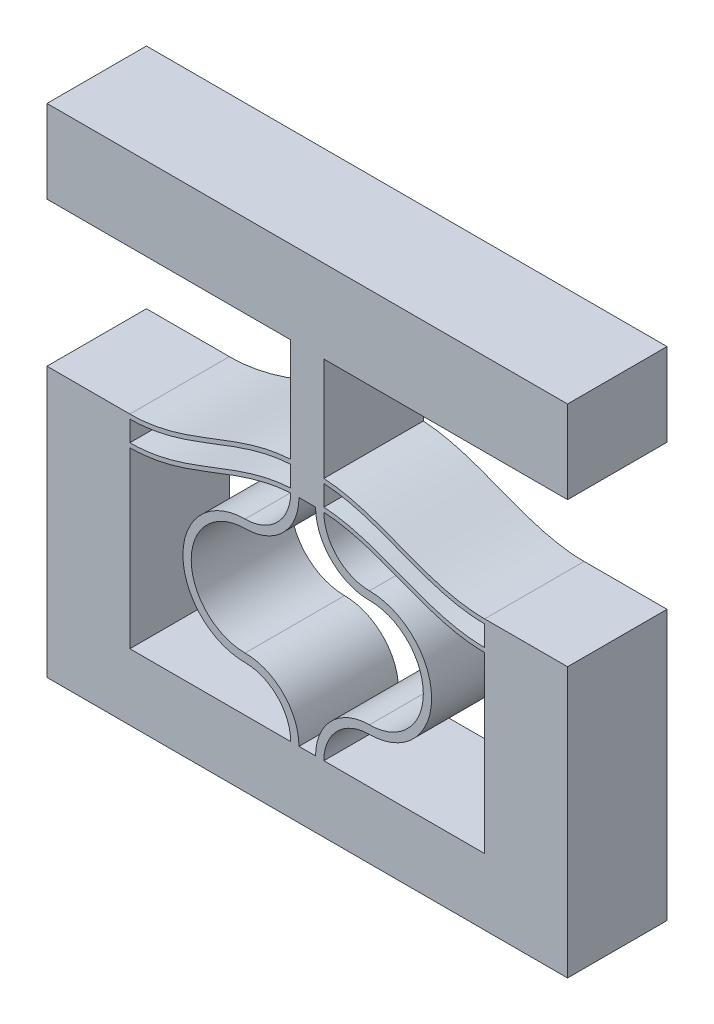
SolidWorks part; units mm, degrees
ref_plane "Front Plane" through (0, 0, 0) normal (0, 0, 1) x (1, 0, 0)
ref_plane "Top Plane" through (0, 0, 0) normal (0, 1, 0) x (1, 0, 0)
ref_plane "Right Plane" through (0, 0, 0) normal (1, 0, 0) x (0, 0, -1)
sketch "Sketch1" plane through (0, 0, 0) normal (0, 0, 1) x (1, 0, 0)
  line L4 (0, 10.5) -> (0, 0)
  line L5 (10.2, 0) -> (10.2, 13) construction
  line L6 (10.2, 13) -> (10.2, 15.9852) construction
  line L17 (9.7, 0) -> (0, 0)
  line L18 (10.7, 0) -> (20.4, 0)
  line L19 (20.4, 0) -> (20.4, 10.5)
  line L20 (10.7, 13.2452) -> (10.7, 14.4852)
  line L21 (9.7, 13.2452) -> (9.7, 14.4852)
  line L22 (10.7, 14.7452) -> (10.7, 15.9852)
  line L23 (10.7, 15.9852) -> (9.7, 15.9852)
  line L24 (9.7, 15.9852) -> (9.7, 14.7452)
  line L31 (-5, 12.26) -> (-5, -4)
  line L32 (-5, -4) -> (25.4, -4)
  line L33 (25.4, -4) -> (25.4, 12.26)
  line L34 (0, 10.76) -> (0, 12)
  line L36 (-5, 12.26) -> (0, 12.26)
  line L37 (25.4, 12.26) -> (20.4, 12.26)
  line L38 (20.4, 10.76) -> (20.4, 12)
  arc A0 (10.2, 13) -> (6.95, 9.75) centre (6.95, 13) cw
  arc A1 (6.95, 9.75) -> (6.95, 3.25) centre (6.95, 6.5) ccw
  arc A2 (6.95, 3.25) -> (10.2, 0) centre (6.95, 0) cw
  arc A3 (9.7, 12.9852) -> (6.95, 10.25) centre (6.95, 13) cw
  arc A4 (6.95, 10.25) -> (6.95, 2.75) centre (6.95, 6.5) ccw
  arc A5 (6.95, 2.75) -> (9.7, 0) centre (6.95, 0) cw
  arc A6 (9.7, 13) -> (6.95, 10.25) centre (6.95, 13) cw construction
  arc A7 (13.45, 3.25) -> (10.2, 0) centre (13.45, 0) ccw
  arc A8 (13.45, 2.75) -> (10.7, 0) centre (13.45, 0) ccw
  arc A9 (13.45, 9.75) -> (13.45, 3.25) centre (13.45, 6.5) cw
  arc A10 (13.45, 10.25) -> (13.45, 2.75) centre (13.45, 6.5) cw
  arc A11 (10.7, 12.9852) -> (13.45, 10.25) centre (13.45, 13) ccw
  arc A12 (10.2, 13) -> (13.45, 9.75) centre (13.45, 13) ccw
  spline S0 degree 4 poles (-2.0399, 10.9987) (-1.9769, 10.9844) (-1.8506, 10.9568) (-1.6594, 10.9185) (-1.4063, 10.8738) (-1.1473, 10.836) (-0.8994, 10.8056) (-0.6275, 10.7825) (-0.4084, 10.7671) (-0.0945, 10.7598) (0.0489, 10.7593) (0.3554, 10.7653) (0.5833, 10.7785) (0.8327, 10.7992) (1.1232, 10.8326) (1.4148, 10.8743) (1.7521, 10.9345) (2.2064, 11.0333) (2.726, 11.1697) (3.2397, 11.3281) (3.7479, 11.5024) (4.1845, 11.6613) (4.5513, 11.7992) (4.9172, 11.9395) (5.2828, 12.0805) (5.7402, 12.2559) (6.427, 12.5125) (7.2136, 12.7819) (8.1107, 13.0284) (9.0261, 13.1932) (9.8075, 13.2661) (10.5925, 13.2661) (11.3739, 13.1932) (12.2893, 13.0284) (13.1864, 12.7819) (13.973, 12.5125) (14.6598, 12.2559) (15.2087, 12.0455) (15.6656, 11.8688) (16.1235, 11.6948) (16.6521, 11.5024) (17.1603, 11.3281) (17.6739, 11.1697) (18.1937, 11.0333) (18.5999, 10.9449) (18.8889, 10.8915) (19.1309, 10.8534) (19.3251, 10.827) (19.5196, 10.8048) (19.7158, 10.7868) (19.909, 10.7733) (20.1017, 10.7642) (20.3513, 10.7593) (20.4943, 10.7598) (20.8085, 10.7671) (21.0274, 10.7825) (21.2994, 10.8056) (21.5473, 10.836) (21.8063, 10.8738) (22.0594, 10.9185) (22.2506, 10.9568) (22.3769, 10.9844) (22.4399, 10.9987) knots 0 0 0 0 0 0.010251 0.020502 0.030753 0.041005 0.05113 0.061255 0.071381 0.081506 0.089265 0.097024 0.112543 0.120302 0.128061 0.143579 0.159098 0.174616 0.201648 0.22868 0.244198 0.259716 0.275235 0.290753 0.306271 0.32179 0.352826 0.40689 0.437927 0.468963 0.5 0.531037 0.562073 0.59311 0.647174 0.67821 0.693729 0.709247 0.740284 0.755802 0.77132 0.798352 0.825384 0.840902 0.856421 0.86418 0.871939 0.879698 0.887457 0.895217 0.902976 0.910735 0.918494 0.928619 0.938745 0.94887 0.958995 0.969247 0.979498 0.989749 1 1 1 1 1 construction
  spline S1 degree 4 poles (0, 10.76) (0.041, 10.76) (0.1243, 10.7608) (0.3554, 10.7653) (0.5833, 10.7785) (0.8327, 10.7992) (1.1232, 10.8326) (1.4148, 10.8743) (1.7521, 10.9345) (2.2064, 11.0333) (2.726, 11.1697) (3.2397, 11.3281) (3.7479, 11.5024) (4.1845, 11.6613) (4.5513, 11.7992) (4.9172, 11.9395) (5.2828, 12.0805) (5.7402, 12.2559) (6.427, 12.5125) (7.2136, 12.7819) (8.1107, 13.0284) (9.0261, 13.1932) (9.8075, 13.2661) (10.5925, 13.2661) (11.3739, 13.1932) (12.2893, 13.0284) (13.1864, 12.7819) (13.973, 12.5125) (14.6598, 12.2559) (15.2087, 12.0455) (15.6656, 11.8688) (16.1235, 11.6948) (16.6521, 11.5024) (17.1603, 11.3281) (17.6739, 11.1697) (18.1937, 11.0333) (18.5999, 10.9449) (18.8889, 10.8915) (19.1309, 10.8534) (19.3251, 10.827) (19.5196, 10.8048) (19.7158, 10.7868) (19.909, 10.7733) (20.1017, 10.7642) (20.2757, 10.7608) (20.359, 10.76) (20.4, 10.76) knots 0.081506 0.081506 0.081506 0.081506 0.081506 0.089265 0.097024 0.112543 0.120302 0.128061 0.143579 0.159098 0.174616 0.201648 0.22868 0.244198 0.259716 0.275235 0.290753 0.306271 0.32179 0.352826 0.40689 0.437927 0.468963 0.5 0.531037 0.562073 0.59311 0.647174 0.67821 0.693729 0.709247 0.740284 0.755802 0.77132 0.798352 0.825384 0.840902 0.856421 0.86418 0.871939 0.879698 0.887457 0.895217 0.902976 0.910735 0.918494 0.918494 0.918494 0.918494 0.918494
  spline S2 degree 4 poles (-2.0399, 12.2387) (-1.9769, 12.2244) (-1.8506, 12.1968) (-1.6594, 12.1585) (-1.4063, 12.1138) (-1.1473, 12.076) (-0.8994, 12.0456) (-0.6275, 12.0225) (-0.4084, 12.0071) (-0.0945, 11.9998) (0.0489, 11.9993) (0.3554, 12.0053) (0.5833, 12.0185) (0.8327, 12.0392) (1.1232, 12.0726) (1.4148, 12.1143) (1.7521, 12.1745) (2.2064, 12.2733) (2.726, 12.4097) (3.2397, 12.5681) (3.7479, 12.7424) (4.1845, 12.9013) (4.5513, 13.0392) (4.9172, 13.1795) (5.2828, 13.3205) (5.7402, 13.4959) (6.427, 13.7525) (7.2136, 14.0219) (8.1107, 14.2684) (9.0261, 14.4332) (9.8075, 14.5061) (10.5925, 14.5061) (11.3739, 14.4332) (12.2893, 14.2684) (13.1864, 14.0219) (13.973, 13.7525) (14.6598, 13.4959) (15.2087, 13.2855) (15.6656, 13.1088) (16.1235, 12.9348) (16.6521, 12.7424) (17.1603, 12.5681) (17.6739, 12.4097) (18.1937, 12.2733) (18.5999, 12.1849) (18.8889, 12.1315) (19.1309, 12.0934) (19.3251, 12.067) (19.5196, 12.0448) (19.7158, 12.0268) (19.909, 12.0133) (20.1017, 12.0042) (20.3513, 11.9993) (20.4943, 11.9998) (20.8085, 12.0071) (21.0274, 12.0225) (21.2994, 12.0456) (21.5473, 12.076) (21.8063, 12.1138) (22.0594, 12.1585) (22.2506, 12.1968) (22.3769, 12.2244) (22.4399, 12.2387) knots 0 0 0 0 0 0.010251 0.020502 0.030753 0.041005 0.05113 0.061255 0.071381 0.081506 0.089265 0.097024 0.112543 0.120302 0.128061 0.143579 0.159098 0.174616 0.201648 0.22868 0.244198 0.259716 0.275235 0.290753 0.306271 0.32179 0.352826 0.40689 0.437927 0.468963 0.5 0.531037 0.562073 0.59311 0.647174 0.67821 0.693729 0.709247 0.740284 0.755802 0.77132 0.798352 0.825384 0.840902 0.856421 0.86418 0.871939 0.879698 0.887457 0.895217 0.902976 0.910735 0.918494 0.928619 0.938745 0.94887 0.958995 0.969247 0.979498 0.989749 1 1 1 1 1 construction
  spline S3 degree 4 poles (0, 12) (0.041, 12) (0.1243, 12.0008) (0.3554, 12.0053) (0.5833, 12.0185) (0.8327, 12.0392) (1.1232, 12.0726) (1.4148, 12.1143) (1.7521, 12.1745) (2.2064, 12.2733) (2.726, 12.4097) (3.2397, 12.5681) (3.7479, 12.7424) (4.1845, 12.9013) (4.5513, 13.0392) (4.9172, 13.1795) (5.2828, 13.3205) (5.7402, 13.4959) (6.427, 13.7525) (7.2136, 14.0219) (8.1107, 14.2684) (9.0261, 14.4332) (9.8075, 14.5061) (10.5925, 14.5061) (11.3739, 14.4332) (12.2893, 14.2684) (13.1864, 14.0219) (13.973, 13.7525) (14.6598, 13.4959) (15.2087, 13.2855) (15.6656, 13.1088) (16.1235, 12.9348) (16.6521, 12.7424) (17.1603, 12.5681) (17.6739, 12.4097) (18.1937, 12.2733) (18.5999, 12.1849) (18.8889, 12.1315) (19.1309, 12.0934) (19.3251, 12.067) (19.5196, 12.0448) (19.7158, 12.0268) (19.909, 12.0133) (20.1017, 12.0042) (20.2757, 12.0008) (20.359, 12) (20.4, 12) knots 0.081506 0.081506 0.081506 0.081506 0.081506 0.089265 0.097024 0.112543 0.120302 0.128061 0.143579 0.159098 0.174616 0.201648 0.22868 0.244198 0.259716 0.275235 0.290753 0.306271 0.32179 0.352826 0.40689 0.437927 0.468963 0.5 0.531037 0.562073 0.59311 0.647174 0.67821 0.693729 0.709247 0.740284 0.755802 0.77132 0.798352 0.825384 0.840902 0.856421 0.86418 0.871939 0.879698 0.887457 0.895217 0.902976 0.910735 0.918494 0.918494 0.918494 0.918494 0.918494
  spline S4 degree 4 poles (-2.0399, 12.4987) (-1.9769, 12.4844) (-1.8506, 12.4568) (-1.6594, 12.4185) (-1.4063, 12.3738) (-1.1473, 12.336) (-0.8994, 12.3056) (-0.6275, 12.2825) (-0.4084, 12.2671) (-0.0945, 12.2598) (0.0489, 12.2593) (0.3554, 12.2653) (0.5833, 12.2785) (0.8327, 12.2992) (1.1232, 12.3326) (1.4148, 12.3743) (1.7521, 12.4345) (2.2064, 12.5333) (2.726, 12.6697) (3.2397, 12.8281) (3.7479, 13.0024) (4.1845, 13.1613) (4.5513, 13.2992) (4.9172, 13.4395) (5.2828, 13.5805) (5.7402, 13.7559) (6.427, 14.0125) (7.2136, 14.2819) (8.1107, 14.5284) (9.0261, 14.6932) (9.8075, 14.7661) (10.5925, 14.7661) (11.3739, 14.6932) (12.2893, 14.5284) (13.1864, 14.2819) (13.973, 14.0125) (14.6598, 13.7559) (15.2087, 13.5455) (15.6656, 13.3688) (16.1235, 13.1948) (16.6521, 13.0024) (17.1603, 12.8281) (17.6739, 12.6697) (18.1937, 12.5333) (18.5999, 12.4449) (18.8889, 12.3915) (19.1309, 12.3534) (19.3251, 12.327) (19.5196, 12.3048) (19.7158, 12.2868) (19.909, 12.2733) (20.1017, 12.2642) (20.3513, 12.2593) (20.4943, 12.2598) (20.8085, 12.2671) (21.0274, 12.2825) (21.2994, 12.3056) (21.5473, 12.336) (21.8063, 12.3738) (22.0594, 12.4185) (22.2506, 12.4568) (22.3769, 12.4844) (22.4399, 12.4987) knots 0 0 0 0 0 0.010251 0.020502 0.030753 0.041005 0.05113 0.061255 0.071381 0.081506 0.089265 0.097024 0.112543 0.120302 0.128061 0.143579 0.159098 0.174616 0.201648 0.22868 0.244198 0.259716 0.275235 0.290753 0.306271 0.32179 0.352826 0.40689 0.437927 0.468963 0.5 0.531037 0.562073 0.59311 0.647174 0.67821 0.693729 0.709247 0.740284 0.755802 0.77132 0.798352 0.825384 0.840902 0.856421 0.86418 0.871939 0.879698 0.887457 0.895217 0.902976 0.910735 0.918494 0.928619 0.938745 0.94887 0.958995 0.969247 0.979498 0.989749 1 1 1 1 1 construction
  spline S5 degree 4 poles (0, 12.26) (0.041, 12.26) (0.1243, 12.2608) (0.3554, 12.2653) (0.5833, 12.2785) (0.8327, 12.2992) (1.1232, 12.3326) (1.4148, 12.3743) (1.7521, 12.4345) (2.2064, 12.5333) (2.726, 12.6697) (3.2397, 12.8281) (3.7479, 13.0024) (4.1845, 13.1613) (4.5513, 13.2992) (4.9172, 13.4395) (5.2828, 13.5805) (5.7402, 13.7559) (6.427, 14.0125) (7.2136, 14.2819) (8.1107, 14.5284) (9.0261, 14.6932) (9.8075, 14.7661) (10.5925, 14.7661) (11.3739, 14.6932) (12.2893, 14.5284) (13.1864, 14.2819) (13.973, 14.0125) (14.6598, 13.7559) (15.2087, 13.5455) (15.6656, 13.3688) (16.1235, 13.1948) (16.6521, 13.0024) (17.1603, 12.8281) (17.6739, 12.6697) (18.1937, 12.5333) (18.5999, 12.4449) (18.8889, 12.3915) (19.1309, 12.3534) (19.3251, 12.327) (19.5196, 12.3048) (19.7158, 12.2868) (19.909, 12.2733) (20.1017, 12.2642) (20.2757, 12.2608) (20.359, 12.26) (20.4, 12.26) knots 0.081506 0.081506 0.081506 0.081506 0.081506 0.089265 0.097024 0.112543 0.120302 0.128061 0.143579 0.159098 0.174616 0.201648 0.22868 0.244198 0.259716 0.275235 0.290753 0.306271 0.32179 0.352826 0.40689 0.437927 0.468963 0.5 0.531037 0.562073 0.59311 0.647174 0.67821 0.693729 0.709247 0.740284 0.755802 0.77132 0.798352 0.825384 0.840902 0.856421 0.86418 0.871939 0.879698 0.887457 0.895217 0.902976 0.910735 0.918494 0.918494 0.918494 0.918494 0.918494
  spline S8 degree 4 poles (-2.0399, 10.7387) (-1.9769, 10.7244) (-1.8506, 10.6968) (-1.6594, 10.6585) (-1.4063, 10.6138) (-1.1473, 10.576) (-0.8994, 10.5456) (-0.6275, 10.5225) (-0.4084, 10.5071) (-0.0945, 10.4998) (0.0489, 10.4993) (0.3554, 10.5053) (0.5833, 10.5185) (0.8327, 10.5392) (1.1232, 10.5726) (1.4148, 10.6143) (1.7521, 10.6745) (2.2064, 10.7733) (2.726, 10.9097) (3.2397, 11.0681) (3.7479, 11.2424) (4.1845, 11.4013) (4.5513, 11.5392) (4.9172, 11.6795) (5.2828, 11.8205) (5.7402, 11.9959) (6.427, 12.2525) (7.2136, 12.5219) (8.1107, 12.7684) (9.0261, 12.9332) (9.8075, 13.0061) (10.5925, 13.0061) (11.3739, 12.9332) (12.2893, 12.7684) (13.1864, 12.5219) (13.973, 12.2525) (14.6598, 11.9959) (15.2087, 11.7855) (15.6656, 11.6088) (16.1235, 11.4348) (16.6521, 11.2424) (17.1603, 11.0681) (17.6739, 10.9097) (18.1937, 10.7733) (18.5999, 10.6849) (18.8889, 10.6315) (19.1309, 10.5934) (19.3251, 10.567) (19.5196, 10.5448) (19.7158, 10.5268) (19.909, 10.5133) (20.1017, 10.5042) (20.3513, 10.4993) (20.4943, 10.4998) (20.8085, 10.5071) (21.0274, 10.5225) (21.2994, 10.5456) (21.5473, 10.576) (21.8063, 10.6138) (22.0594, 10.6585) (22.2506, 10.6968) (22.3769, 10.7244) (22.4399, 10.7387) knots 0 0 0 0 0 0.010251 0.020502 0.030753 0.041005 0.05113 0.061255 0.071381 0.081506 0.089265 0.097024 0.112543 0.120302 0.128061 0.143579 0.159098 0.174616 0.201648 0.22868 0.244198 0.259716 0.275235 0.290753 0.306271 0.32179 0.352826 0.40689 0.437927 0.468963 0.5 0.531037 0.562073 0.59311 0.647174 0.67821 0.693729 0.709247 0.740284 0.755802 0.77132 0.798352 0.825384 0.840902 0.856421 0.86418 0.871939 0.879698 0.887457 0.895217 0.902976 0.910735 0.918494 0.928619 0.938745 0.94887 0.958995 0.969247 0.979498 0.989749 1 1 1 1 1 construction
  spline S9 degree 4 poles (0, 10.5) (0.041, 10.5) (0.1243, 10.5008) (0.3554, 10.5053) (0.5833, 10.5185) (0.8327, 10.5392) (1.1232, 10.5726) (1.4148, 10.6143) (1.7521, 10.6745) (2.2064, 10.7733) (2.726, 10.9097) (3.2397, 11.0681) (3.7479, 11.2424) (4.1845, 11.4013) (4.5513, 11.5392) (4.9172, 11.6795) (5.2828, 11.8205) (5.7402, 11.9959) (6.427, 12.2525) (7.2136, 12.5219) (8.1107, 12.7684) (9.0261, 12.9332) (9.8075, 13.0061) (10.5925, 13.0061) (11.3739, 12.9332) (12.2893, 12.7684) (13.1864, 12.5219) (13.973, 12.2525) (14.6598, 11.9959) (15.2087, 11.7855) (15.6656, 11.6088) (16.1235, 11.4348) (16.6521, 11.2424) (17.1603, 11.0681) (17.6739, 10.9097) (18.1937, 10.7733) (18.5999, 10.6849) (18.8889, 10.6315) (19.1309, 10.5934) (19.3251, 10.567) (19.5196, 10.5448) (19.7158, 10.5268) (19.909, 10.5133) (20.1017, 10.5042) (20.2757, 10.5008) (20.359, 10.5) (20.4, 10.5) knots 0.081506 0.081506 0.081506 0.081506 0.081506 0.089265 0.097024 0.112543 0.120302 0.128061 0.143579 0.159098 0.174616 0.201648 0.22868 0.244198 0.259716 0.275235 0.290753 0.306271 0.32179 0.352826 0.40689 0.437927 0.468963 0.5 0.531037 0.562073 0.59311 0.647174 0.67821 0.693729 0.709247 0.740284 0.755802 0.77132 0.798352 0.825384 0.840902 0.856421 0.86418 0.871939 0.879698 0.887457 0.895217 0.902976 0.910735 0.918494 0.918494 0.918494 0.918494 0.918494
  dimension "D4" = 0.26
  dimension "D6" = 4
  dimension "D1" = 13
  dimension "D2" = 0.5
  dimension "D3" = 0.26
  dimension "D7" = 5
  dimension "D5" = 1.5
extrude "Boss-Extrude1" add sketch "Sketch1" along normal blind 6
sketch "Sketch4" plane through (0, 15.9852, 0) normal (0, 1, 0) x (1, 0, 0)
  line L24 (10.7, 0) -> (9.7, 0)
  line L25 (9.7, 0) -> (9.7, -6)
  line L26 (10.7, 0) -> (9.7, 0)
  line L27 (10.7, -6) -> (10.7, 0)
  line L29 (9.7, 0) -> (9.7, -6)
  line L31 (10.7, -6) -> (10.7, 0)
  line L32 (9.7, -6) -> (10.7, -6)
  line L33 (9.7, -6) -> (10.7, -6)
  dimension "D1" = 0
extrude "Boss-Extrude2" add sketch "Sketch4" along normal blind 5
mirror "Mirror3" [suppressed]
ref_plane "Plane1" through (10.2, 0, 0) normal (-1, 0, 0) x (0, 0, 1)
split "Split2" trim tools "Plane1" bodies to split 179 102 resulting bodies 225
sketch "Sketch7" plane through (10.2, 0, 0) normal (-1, 0, 0) x (0, 0, 1)
  line L4 (0, 13) -> (6, 13)
  line L12 (0, 13) -> (6, 13)
  line L13 (0, 13) -> (6, 13)
  line L14 (6, 13) -> (6, 20.9852)
  line L15 (6, 13) -> (6, 20.9852)
  line L20 (6, 0) -> (0, 0)
  line L22 (6, 0) -> (0, 0)
  line L23 (0, -4) -> (6, -4)
  line L27 (0, -4) -> (6, -4)
  line L31 (6, 20.9852) -> (0, 20.9852)
  line L33 (0, 20.9852) -> (0, 13)
  line L34 (0, 20.9852) -> (0, 13)
  line L36 (6, -4) -> (6, 0)
  line L38 (0, 13) -> (6, 13)
  line L39 (0, 13) -> (6, 13)
  line L40 (6, 13) -> (6, 20.9852)
  line L41 (6, 13) -> (6, 20.9852)
  line L51 (6, 20.9852) -> (0, 20.9852)
  line L52 (6, 20.9852) -> (0, 20.9852)
  line L53 (0, 20.9852) -> (0, 13)
  line L54 (0, 20.9852) -> (0, 13)
  line L55 (0, 13) -> (6, 13)
  line L59 (6, -4) -> (6, 0)
  line L60 (0, 0) -> (0, -4)
  line L61 (0, 0) -> (0, -4)
  line L62 (6, 13) -> (6, 20.9852)
  line L64 (6, 13) -> (6, 20.9852)
  line L66 (6, 20.9852) -> (0, 20.9852)
  line L67 (6, 20.9852) -> (0, 20.9852)
  line L68 (0, 20.9852) -> (0, 13)
  line L69 (0, 20.9852) -> (0, 13)
  line L70 (6, 20.9852) -> (0, 20.9852)
  dimension "D1" = 0
  dimension "D2" = 0
  dimension "D3" = 0
  dimension "D4" = 0
extrude "Boss-Extrude3" add sketch "Sketch7" along normal blind 0.5
mirror "Mirror2" about plane through (9.7, 0, 0) normal (-1, 0, 0) of bodies 226
sketch "Sketch8" plane through (0, 0, 6) normal (0, 0, 1) x (1, 0, 0)
  line L0 (25.4, 12.26) -> (20.4, 12.26) construction
  line L1 (-6, 25.9852) -> (25.4, 25.9852)
  line L2 (-6, 25.9852) -> (-6, 20.9852)
  line L3 (-6, 20.9852) -> (25.4, 20.9852)
  line L4 (25.4, 25.9852) -> (25.4, 20.9852)
  line L5 (25.4, -4) -> (25.4, 12.26) construction
  line L6 (-6, -4) -> (-6, 12.26) construction
  line L7 (8.7, 20.9852) -> (10.7, 20.9852) construction
extrude "Boss-Extrude4" add sketch "Sketch8" against normal up to surface (6 mm away) up to face at (9.7, 11.4986, 0)
